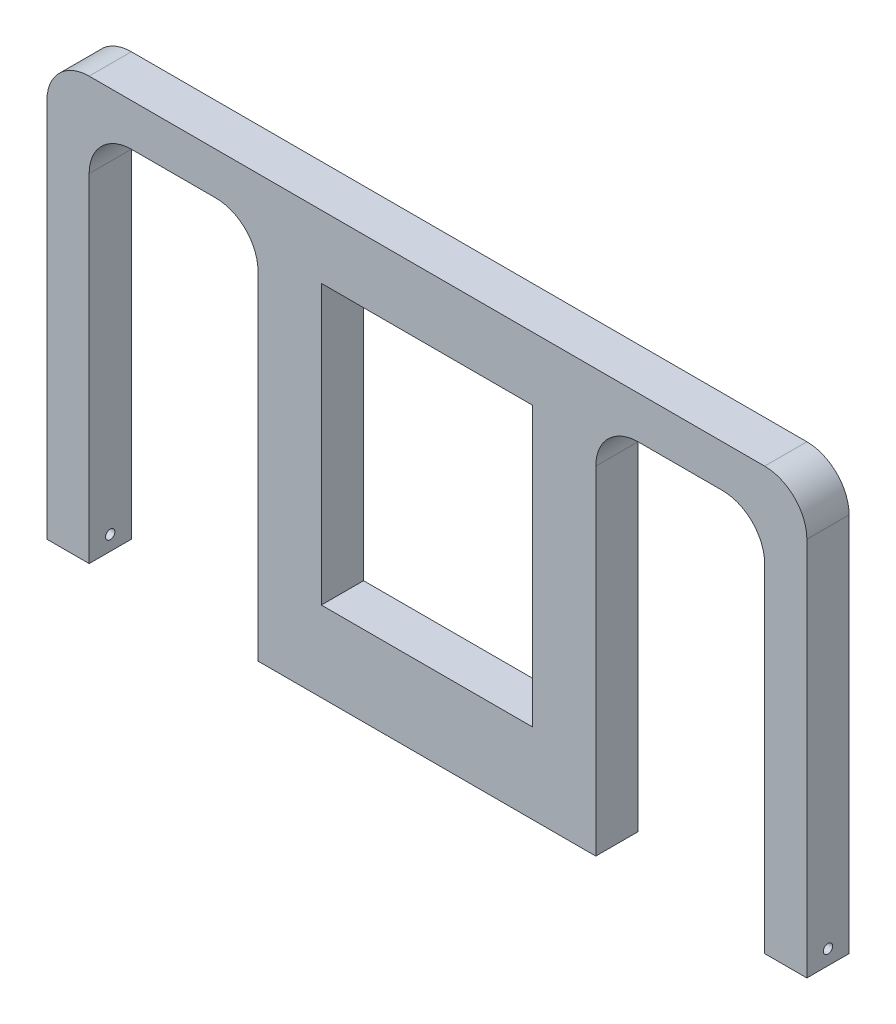
SolidWorks part; units mm, degrees
ref_plane "Front Plane" through (0, 0, 0) normal (0, 0, 1) x (1, 0, 0)
ref_plane "Top Plane" through (0, 0, 0) normal (0, 1, 0) x (1, 0, 0)
ref_plane "Right Plane" through (0, 0, 0) normal (1, 0, 0) x (0, 0, -1)
sketch "Sketch1" plane through (0, 0, 0) normal (0, 1, 0) x (1, 0, 0)
  line L0 (-101.6, 0) -> (101.6, 0) construction
  line L1 (-114.3, 0) -> (-101.6, 0)
  line L2 (-114.3, 0) -> (-114.3, -12.7)
  line L3 (-114.3, -12.7) -> (-101.6, -12.7)
  line L4 (-101.6, 0) -> (-101.6, -12.7)
  line L5 (114.3, -12.7) -> (101.6, -12.7)
  line L6 (114.3, -12.7) -> (114.3, 0)
  line L7 (114.3, 0) -> (101.6, 0)
  line L8 (101.6, -12.7) -> (101.6, 0)
  point P10 (0, 0)
  point P12 (0, 0)
  point P13 (0, 0)
  dimension "D1" = 12.7
  dimension "D2" = 203.2
extrude "Boss-Extrude1" add sketch "Sketch1" along normal blind 114.3
sketch "Sketch2" plane through (-114.3, 0, 0) normal (-1, 0, 0) x (0, 0, 1)
  line L0 (12.7, 114.3) -> (12.7, 0) construction
  line L1 (0, 114.3) -> (12.7, 114.3)
  line L2 (0, 114.3) -> (0, 127)
  line L3 (0, 127) -> (12.7, 127)
  line L4 (12.7, 114.3) -> (12.7, 127)
extrude "Boss-Extrude2" add sketch "Sketch2" against normal blind 228.6
sketch "Sketch3" plane through (0, 114.3, 0) normal (0, -1, 0) x (1, 0, 0)
  line L0 (-101.6, 6.35) -> (101.6, 6.35) construction
  line L1 (-101.6, 12.7) -> (-101.6, 0) construction
  line L2 (101.6, 0) -> (101.6, 12.7) construction
  line L3 (101.6, 0) -> (-101.6, 0) construction
  line L4 (50.8, 12.7) -> (-50.8, 12.7)
  line L5 (50.8, 12.7) -> (50.8, 0)
  line L6 (50.8, 0) -> (-50.8, 0)
  line L7 (-50.8, 12.7) -> (-50.8, 0)
  line L8 (50.8, 12.7) -> (-50.8, 0) construction
  line L9 (50.8, 0) -> (-50.8, 12.7) construction
  point P6 (0, 6.35)
  dimension "D1" = 101.6
extrude "Boss-Extrude3" add sketch "Sketch3" along normal blind 114.3
sketch "Sketch4" plane through (114.3, 0, 0) normal (1, 0, 0) x (0, 0, -1)
  line L0 (-12.7, 4.445) -> (0, 4.445) construction
  line L1 (-12.7, 0) -> (-12.7, 127) construction
  line L2 (0, 127) -> (0, 0) construction
  line L3 (-12.7, 0) -> (0, 0) construction
  circle A0 centre (-6.35, 4.445) radius 1.397
  point P8 (0, 0)
  point P9 (-6.35, 4.445)
  dimension "D1" = 2.794
  dimension "D2" = 4.445
extrude "Cut-Extrude1" cut sketch "Sketch4" against normal up to next (12.7 mm away)
mirror "Mirror1" about plane through (0, 0, 0) normal (1, 0, 0) of "Cut-Extrude1"
sketch "Sketch5" plane through (0, 0, 0) normal (0, 0, -1) x (-1, 0, 0)
  line L0 (-101.6, 114.3) -> (-101.6, 101.6)
  line L1 (-101.6, 114.3) -> (-101.6, 0) construction
  line L2 (-101.6, 114.3) -> (-88.9, 114.3)
  line L3 (-101.6, 114.3) -> (-50.8, 114.3) construction
  line L4 (-50.8, 114.3) -> (-63.5, 114.3)
  line L5 (-50.8, 114.3) -> (-50.8, 101.6)
  line L6 (-50.8, 0) -> (-50.8, 114.3) construction
  arc A0 (-101.6, 101.6) -> (-88.9, 114.3) centre (-88.9, 101.6) cw
  arc A1 (-50.8, 101.6) -> (-63.5, 114.3) centre (-63.5, 101.6) ccw
  dimension "D1" = 12.7
extrude "Boss-Extrude4" add sketch "Sketch5" against normal blind 12.7
mirror "Mirror2" about plane through (0, 0, 0) normal (1, 0, 0) of "Boss-Extrude4"
sketch "Sketch6" plane through (0, 0, 0) normal (0, 0, -1) x (-1, 0, 0)
  line L0 (-114.3, 127) -> (-114.3, 114.3)
  line L1 (-114.3, 127) -> (-114.3, 0) construction
  line L2 (-114.3, 127) -> (-101.6, 127)
  line L3 (-114.3, 127) -> (114.3, 127) construction
  arc A0 (-114.3, 114.3) -> (-101.6, 127) centre (-101.6, 114.3) cw
  dimension "D1" = 12.7
extrude "Cut-Extrude2" cut sketch "Sketch6" against normal blind 12.7
mirror "Mirror3" about plane through (0, 0, 0) normal (1, 0, 0) of "Cut-Extrude2"
sketch "Sketch7" plane through (0, 0, 0) normal (0, 0, -1) x (-1, 0, 0)
  line L0 (-101.6, 127) -> (101.6, 127) construction
  line L1 (-31.75, 107.95) -> (31.75, 107.95)
  line L2 (-31.75, 107.95) -> (-31.75, 24.13)
  line L3 (-31.75, 24.13) -> (31.75, 24.13)
  line L4 (31.75, 107.95) -> (31.75, 24.13)
  line L5 (-31.75, 107.95) -> (31.75, 24.13) construction
  line L6 (-31.75, 24.13) -> (31.75, 107.95) construction
  line L7 (-50.8, 0) -> (-50.8, 101.6) construction
  line L8 (50.8, 0) -> (50.8, 101.6) construction
  line L9 (50.8, 0) -> (-50.8, 0) construction
  point P0 (0, 66.04)
  dimension "D1" = 19.05
  dimension "D2" = 19.05
  dimension "D3" = 19.05
  dimension "D4" = 24.13
extrude "Cut-Extrude3" cut sketch "Sketch7" against normal blind 12.7
